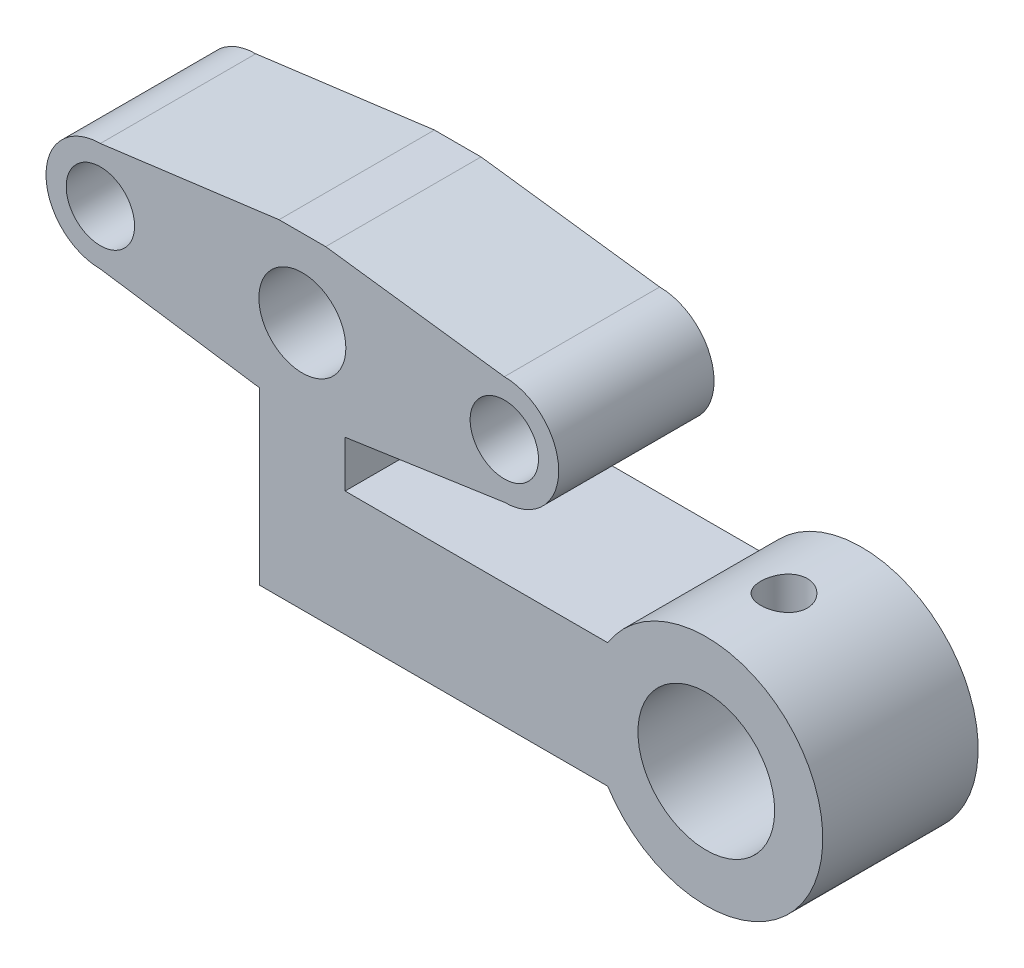
SolidWorks part; units mm, degrees
ref_plane "Plan de face" through (0, 0, 0) normal (0, 0, 1) x (1, 0, 0)
ref_plane "Plan de dessus" through (0, 0, 0) normal (0, 1, 0) x (1, 0, 0)
ref_plane "Plan de droite" through (0, 0, 0) normal (1, 0, 0) x (0, 0, -1)
sketch "Esquisse1" plane through (0, 0, 0) normal (0, 0, 1) x (1, 0, 0)
  line L0 (-13, 0) -> (13, 0) construction
  line L1 (13, 0) -> (13, -12) construction
  line L2 (13, -12) -> (26, -12) construction
  line L3 (-1.5, 5) -> (1.5, 5)
  line L4 (0, 0) -> (0, 5) construction
  line L5 (-13, -3.5) -> (-2.75, -5)
  line L6 (2.75, -5) -> (13, -3.5)
  line L7 (0, 0) -> (0, -12) construction
  line L8 (26, -12) -> (0, -12) construction
  line L9 (-2.75, -5) -> (2.75, -5)
  line L10 (-2.75, -5) -> (-2.75, -16)
  line L11 (-2.75, -16) -> (2.75, -16)
  line L12 (2.75, -5) -> (2.75, -16)
  line L13 (-1.5, 5) -> (-13, 3.5)
  line L14 (0, -8) -> (21.6, -8)
  line L15 (0, -8) -> (0, -16)
  line L16 (0, -16) -> (21.6, -16)
  line L17 (21.6, -8) -> (21.6, -16)
  line L18 (1.5, 5) -> (13, 3.5)
  circle A0 centre (0, 0) radius 2.8
  circle A3 centre (26, -12) radius 4.4
  arc A4 (-13, 3.5) -> (-13, -3.5) centre (-13, 0) ccw
  arc A5 (13, -3.5) -> (13, 3.5) centre (13, 0) ccw
  circle A7 centre (26, -12) radius 7.5
  point P15 (0, -5)
  dimension "D1" = 5.6
  dimension "D2" = 26
  dimension "D6" = 8.8
  dimension "D7" = 7
  dimension "D8" = 5
  dimension "D9" = 15
  dimension "D4" = 12
  dimension "D5" = 13
  dimension "D10" = 5.5
  dimension "D11" = 8
  dimension "D12" = 5
  dimension "D13" = 3
extrude "Boss.-Extru.1" add sketch "Esquisse1" along normal blind 10
ref_plane "Plan1" through (0, -4.5, 0) normal (0, 1, 0) x (1, 0, 0)
sketch "Esquisse2" plane through (0, -4.5, 0) normal (0, 1, 0) x (1, 0, 0)
  line L0 (0, 0) -> (0, -10) construction
  line L1 (0, -5) -> (26, -5) construction
  circle A0 centre (26, -5) radius 1.5
  point P5 (0, -5)
  dimension "D1" = 3
  dimension "D2" = 10
  dimension "D3" = 26
extrude "Enlèv. mat.-Extru.1" cut sketch "Esquisse2" against normal up to next
sketch "Esquisse4" plane through (0, 0, 10) normal (0, 0, 1) x (1, 0, 0)
  line L0 (-13, 0) -> (13, 0) construction
  circle A0 centre (-13, 0) radius 2.2
  circle A1 centre (13, 0) radius 2.2
  dimension "D2" = 4.4
  dimension "D1" = 26
extrude "Enlèv. mat.-Extru.2" cut sketch "Esquisse4" against normal blind 9
